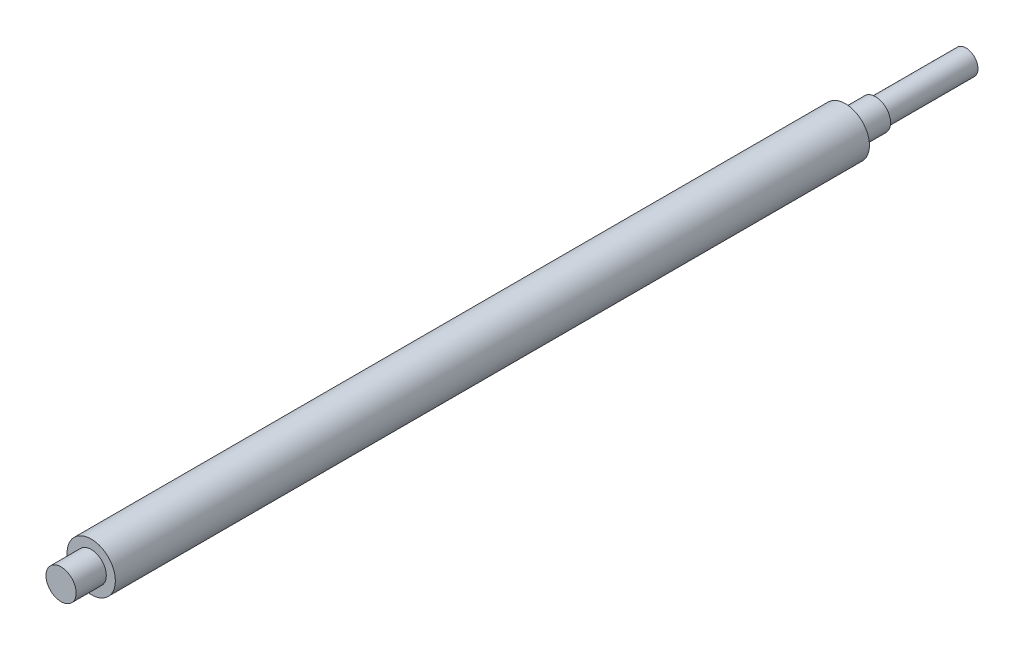
SolidWorks part; units mm, degrees
material "1.0037 (S235JR)"
ref_plane "Front Plane" through (0, 0, 0) normal (0, 0, 1) x (1, 0, 0)
ref_plane "Top Plane" through (0, 0, 0) normal (0, 1, 0) x (1, 0, 0)
ref_plane "Right Plane" through (0, 0, 0) normal (1, 0, 0) x (0, 0, -1)
sketch "Sketch1" plane through (0, 0, 0) normal (0, 0, 1) x (1, 0, 0)
  circle A0 centre (0, 0) radius 8
  dimension "D1" = 16
extrude "Boss-Extrude1" add sketch "Sketch1" along normal blind 250
sketch "Sketch2" plane through (0, 0, 250) normal (0, 0, 1) x (1, 0, 0)
  circle A0 centre (0, 0) radius 5
  dimension "D1" = 10
extrude "Boss-Extrude2" add sketch "Sketch2" along normal blind 10
sketch "Sketch3" plane through (0, 0, 0) normal (0, 0, -1) x (-1, 0, 0)
  circle A0 centre (0, 0) radius 5
  dimension "D1" = 10
extrude "Boss-Extrude3" add sketch "Sketch3" along normal blind 10
sketch "Sketch4" plane through (0, 0, -10) normal (0, 0, -1) x (-1, 0, 0)
  circle A0 centre (0, 0) radius 4
  dimension "D1" = 8
extrude "Boss-Extrude4" add sketch "Sketch4" along normal blind 30
